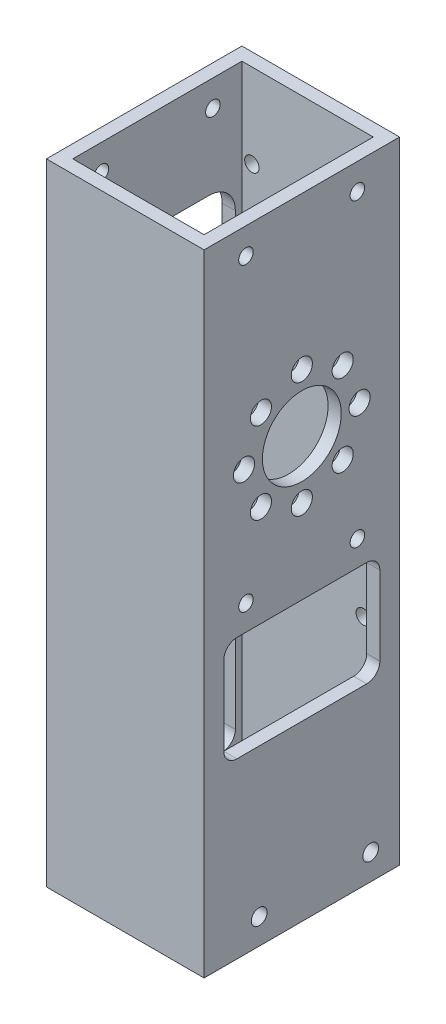
SolidWorks part; units mm, degrees
material "6061 Alloy"
ref_plane "Front" through (0, 0, 0) normal (0, 0, 1) x (1, 0, 0)
ref_plane "Top" through (0, 0, 0) normal (0, 1, 0) x (1, 0, 0)
ref_plane "Right" through (0, 0, 0) normal (1, 0, 0) x (0, 0, -1)
sketch "Sketch1" plane through (0, 0, 0) normal (0, 1, 0) x (1, 0, 0)
  line L0 (-15.875, 20.447) -> (15.875, 20.447)
  line L1 (-19.05, -23.622) -> (19.05, -23.622)
  line L2 (-19.05, -23.622) -> (-19.05, 23.622)
  line L3 (-19.05, 23.622) -> (19.05, 23.622)
  line L4 (19.05, -23.622) -> (19.05, 23.622)
  line L5 (-19.05, -23.622) -> (19.05, 23.622) construction
  line L6 (-19.05, 23.622) -> (19.05, -23.622) construction
  line L7 (15.875, -20.447) -> (15.875, 20.447)
  line L8 (-15.875, -20.447) -> (15.875, -20.447)
  line L9 (-15.875, -20.447) -> (-15.875, 20.447)
  point P0 (0, 0)
  dimension "D1" = 38.1
  dimension "D2" = 47.244
  dimension "D3" = 3.175
extrude "Boss-Extrude1" add sketch "Sketch1" along normal blind 152.4
sketch "Sketch2" plane through (15.875, 0, 0) normal (-1, 0, 0) x (0, 0, 1)
  circle A0 centre (-16.6454, 6.2154) radius 1.8986
  circle A1 centre (10.3003, 6.1824) radius 1.8986
  dimension "D1" = 3.7973
extrude "Cut-Extrude1" cut sketch "Sketch2" against normal through all both and the other way through all
sketch "Sketch4" plane through (-19.05, 0, 0) normal (-1, 0, 0) x (0, 0, 1)
  line L0 (-23.622, 152.4) -> (-23.622, 0) construction
  line L1 (15.6845, 10.16) -> (-15.6845, 10.16)
  line L2 (18.8595, 13.335) -> (18.8595, 64.135)
  line L3 (15.6845, 67.31) -> (-15.6845, 67.31)
  line L4 (-18.8595, 13.335) -> (-18.8595, 64.135)
  line L5 (18.8595, 10.16) -> (-18.8595, 67.31) construction
  line L6 (18.8595, 67.31) -> (-18.8595, 10.16) construction
  line L7 (23.622, 152.4) -> (23.622, 0) construction
  line L8 (-23.622, 0) -> (23.622, 0) construction
  arc A0 (-15.6845, 67.31) -> (-18.8595, 64.135) centre (-15.6845, 64.135) ccw
  arc A1 (18.8595, 64.135) -> (15.6845, 67.31) centre (15.6845, 64.135) ccw
  arc A2 (15.6845, 10.16) -> (18.8595, 13.335) centre (15.6845, 13.335) ccw
  arc A3 (-15.6845, 10.16) -> (-18.8595, 13.335) centre (-15.6845, 13.335) cw
  point P4 (0, 38.735)
  dimension "D4" = 3.175
  dimension "D1" = 4.7625
  dimension "D2" = 4.7625
  dimension "D3" = 10.16
  dimension "D5" = 57.15
extrude "Cut-Extrude3" cut sketch "Sketch4" against normal blind 3.175
sketch "Sketch5" plane through (19.05, 0, 0) normal (1, 0, 0) x (0, 0, -1)
  line L0 (23.622, 152.4) -> (23.622, 0) construction
  line L1 (15.6845, 67.31) -> (-15.6845, 67.31)
  line L2 (18.8595, 64.135) -> (18.8595, 45.085)
  line L3 (15.6845, 41.91) -> (-15.6845, 41.91)
  line L4 (-18.8595, 64.135) -> (-18.8595, 45.085)
  line L5 (18.8595, 67.31) -> (-18.8595, 41.91) construction
  line L6 (18.8595, 41.91) -> (-18.8595, 67.31) construction
  line L7 (-23.622, 152.4) -> (-23.622, 0) construction
  line L10 (23.622, 0) -> (-23.622, 0) construction
  arc A0 (-15.6845, 41.91) -> (-18.8595, 45.085) centre (-15.6845, 45.085) cw
  arc A1 (-15.6845, 67.31) -> (-18.8595, 64.135) centre (-15.6845, 64.135) ccw
  arc A2 (18.8595, 45.085) -> (15.6845, 41.91) centre (15.6845, 45.085) cw
  arc A3 (15.6845, 67.31) -> (18.8595, 64.135) centre (15.6845, 64.135) cw
  point P4 (0, 54.61)
  dimension "D5" = 3.175
  dimension "D1" = 4.7625
  dimension "D2" = 4.7625
  dimension "D3" = 67.31
  dimension "D4" = 25.4
extrude "Cut-Extrude4" cut sketch "Sketch5" against normal blind 3.175
sketch "Sketch6" plane through (15.875, 0, 0) normal (-1, 0, 0) x (0, 0, 1)
  line L0 (0, 101.6) -> (0, 0) construction
  line L1 (0, 87.63) -> (0, 101.6) construction
  circle A0 centre (0, 101.6) radius 9.525
  circle A1 centre (0, 87.63) radius 2.5527
  circle A2 centre (-9.8783, 91.7217) radius 2.5527
  circle A3 centre (-13.97, 101.6) radius 2.5527
  circle A4 centre (-9.8783, 111.4783) radius 2.5527
  circle A5 centre (0, 115.57) radius 2.5527
  circle A6 centre (9.8783, 111.4783) radius 2.5527
  circle A7 centre (13.97, 101.6) radius 2.5527
  circle A8 centre (9.8783, 91.7217) radius 2.5527
  point P22 (0, 101.6)
  dimension "D1" = 19.05
  dimension "D3" = 5.1054
  dimension "D2" = 101.6
  dimension "D4" = 13.97
  dimension "D6" = 0
  dimension "D5" = 8
extrude "Cut-Extrude5" cut sketch "Sketch6" against normal blind 3.175
sketch "Sketch7" plane through (-19.05, 0, 0) normal (-1, 0, 0) x (0, 0, 1)
  line L0 (23.622, 152.4) -> (23.622, 0) construction
  line L1 (-12.5095, 77.47) -> (12.5095, 77.47)
  line L2 (-18.8595, 83.82) -> (-18.8595, 121.92)
  line L3 (-12.5095, 128.27) -> (12.5095, 128.27)
  line L4 (18.8595, 83.82) -> (18.8595, 121.92)
  line L5 (-18.8595, 77.47) -> (18.8595, 128.27) construction
  line L6 (-18.8595, 128.27) -> (18.8595, 77.47) construction
  line L7 (-23.622, 152.4) -> (-23.622, 0) construction
  line L8 (16.51, 67.31) -> (-16.51, 67.31) construction
  arc A0 (-18.8595, 121.92) -> (-12.5095, 128.27) centre (-12.5095, 121.92) cw
  arc A1 (12.5095, 128.27) -> (18.8595, 121.92) centre (12.5095, 121.92) cw
  arc A2 (12.5095, 77.47) -> (18.8595, 83.82) centre (12.5095, 83.82) ccw
  arc A3 (-12.5095, 77.47) -> (-18.8595, 83.82) centre (-12.5095, 83.82) cw
  point P4 (0, 102.87)
  dimension "D5" = 6.35
  dimension "D1" = 50.8
  dimension "D2" = 4.7625
  dimension "D3" = 4.7625
  dimension "D4" = 10.16
extrude "Cut-Extrude6" cut sketch "Sketch7" against normal blind 3.175
sketch "Sketch8" plane through (19.05, 0, 0) normal (1, 0, 0) x (0, 0, -1)
  point P1 (-13.5004, 73.406)
  point P6 (13.4236, 146.05)
  point P7 (-13.5004, 146.05)
  point P9 (13.4236, 73.406)
hole_wizard "#6-32 Tapped Hole1" positions "3DSketch1" profile "Sketch9" tap size "#6-32" standard "ANSI Inch" end condition through all
sketch3d "3DSketch1"
  point P0 (19.05, 73.406, -13.4236)
  point P3 (19.05, 73.406, 13.5004)
  point P6 (19.05, 146.05, 13.5004)
  point P9 (19.05, 146.05, -13.4236)
sketch "Sketch9" plane through (19.05, 73.406, -13.4236) normal (0, 1, 0) x (0, 0, -1)
  line L0 (0, 0) -> (0, 38.1)
  line L1 (0, 38.1) -> (1.7526, 38.1)
  line L2 (1.7526, 38.1) -> (1.7526, 0)
  line L5 (1.7526, 0) -> (0, 0)
  line L11 (0, -6.35) -> (0, 107.95) construction
  dimension "Thread Major Dia." = 3.5052
  dimension "Thru Tap Drill Depth" = 38.1
sketch "Sketch11" plane through (0, 0, -23.622) normal (0, 0, -1) x (-1, 0, 0)
  line L0 (-5.5796, 136.6393) -> (5.5796, 136.6393) construction
  line L1 (0, 136.6393) -> (0, 152.4) construction
  line L2 (-19.05, 152.4) -> (19.05, 152.4) construction
sketch "Sketch15" plane through (0, 0, -23.622) normal (0, 0, -1) x (-1, 0, 0)
  line L0 (-13.462, 0) -> (-13.462, 152.4) construction
  line L1 (-19.05, 0) -> (19.05, 0) construction
  line L2 (-19.05, 152.4) -> (19.05, 152.4) construction
  line L3 (13.462, 152.4) -> (13.462, 0) construction
  line L4 (-19.05, 152.4) -> (-19.05, 0) construction
  line L5 (19.05, 152.4) -> (19.05, 0) construction
  line L6 (-13.462, 50.8) -> (13.462, 50.8) construction
  line L7 (-13.462, 76.2) -> (13.462, 76.2) construction
  line L8 (-13.462, 132.08) -> (13.462, 132.08) construction
  line L9 (19.05, 0) -> (-19.05, 0) construction
  circle A0 centre (-13.462, 50.8) radius 1.7526
  circle A1 centre (13.462, 50.8) radius 1.7526
  circle A2 centre (-13.462, 76.2) radius 1.7526
  circle A3 centre (13.462, 76.2) radius 1.7526
  circle A4 centre (-13.462, 132.08) radius 1.7526
  circle A5 centre (13.462, 132.08) radius 1.7526
  dimension "D1" = 5.588
  dimension "D2" = 5.588
  dimension "D3" = 50.8
  dimension "D4" = 76.2
  dimension "D5" = 132.08
extrude "Cut-Extrude10" cut sketch "Sketch15" against normal up to next
